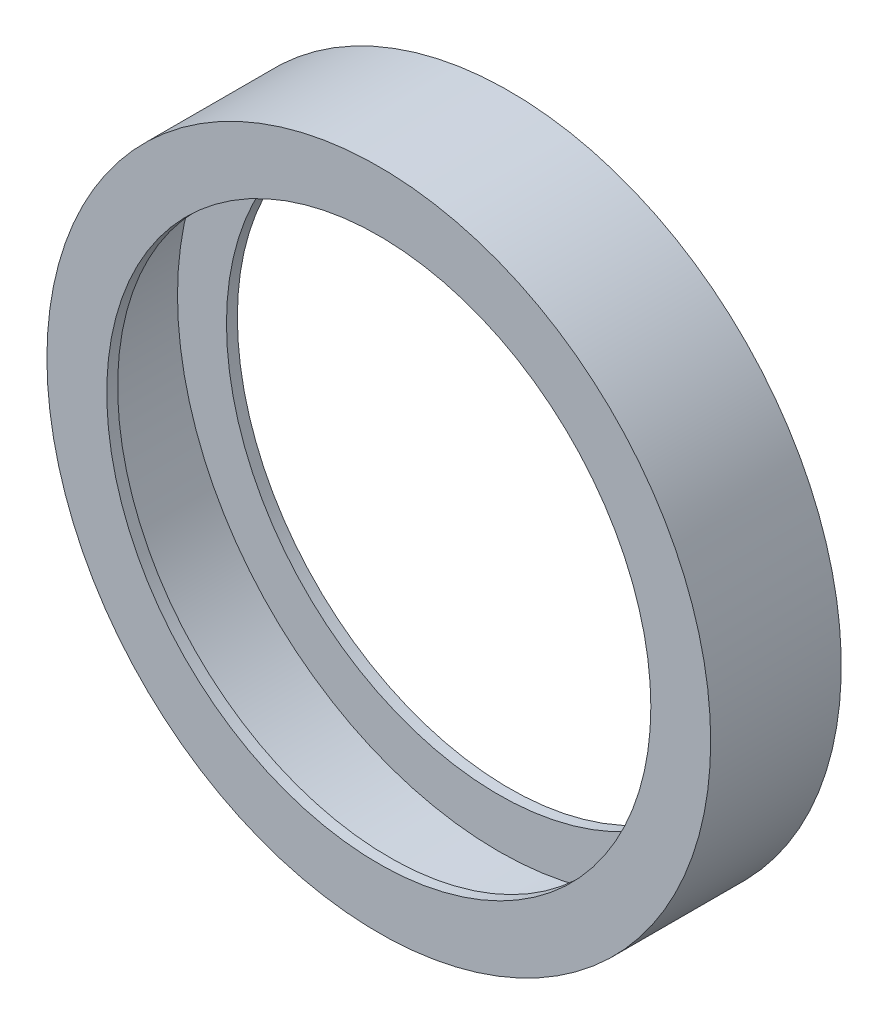
SolidWorks part; units mm, degrees
ref_plane "Front Plane" through (0, 0, 0) normal (0, 0, 1) x (1, 0, 0)
ref_plane "Top Plane" through (0, 0, 0) normal (0, 1, 0) x (1, 0, 0)
ref_plane "Right Plane" through (0, 0, 0) normal (1, 0, 0) x (0, 0, -1)
sketch "Sketch1" plane through (0, 0, 0) normal (0, 0, 1) x (1, 0, 0)
  circle A0 centre (0, 0) radius 30.5
  circle A2 centre (0, 0) radius 25
  dimension "D1" = 61
  dimension "D3" = 50
extrude "Boss-Extrude1" add sketch "Sketch1" along normal blind 1
sketch "Sketch2" plane through (0, 0, 0) normal (0, 0, -1) x (-1, 0, 0)
  circle A0 centre (0, 0) radius 30.5
  circle A1 centre (0, 0) radius 29.5
  dimension "D1" = 61
  dimension "D2" = 59
extrude "Boss-Extrude2" add sketch "Sketch2" along normal blind 10
sketch "Sketch3" plane through (0, 0, -10) normal (0, 0, -1) x (-1, 0, 0)
  circle A0 centre (0, 0) radius 30.5
  circle A1 centre (0, 0) radius 25
  dimension "D1" = 61
  dimension "D2" = 50
extrude "Boss-Extrude3" add sketch "Sketch3" along normal blind 1
